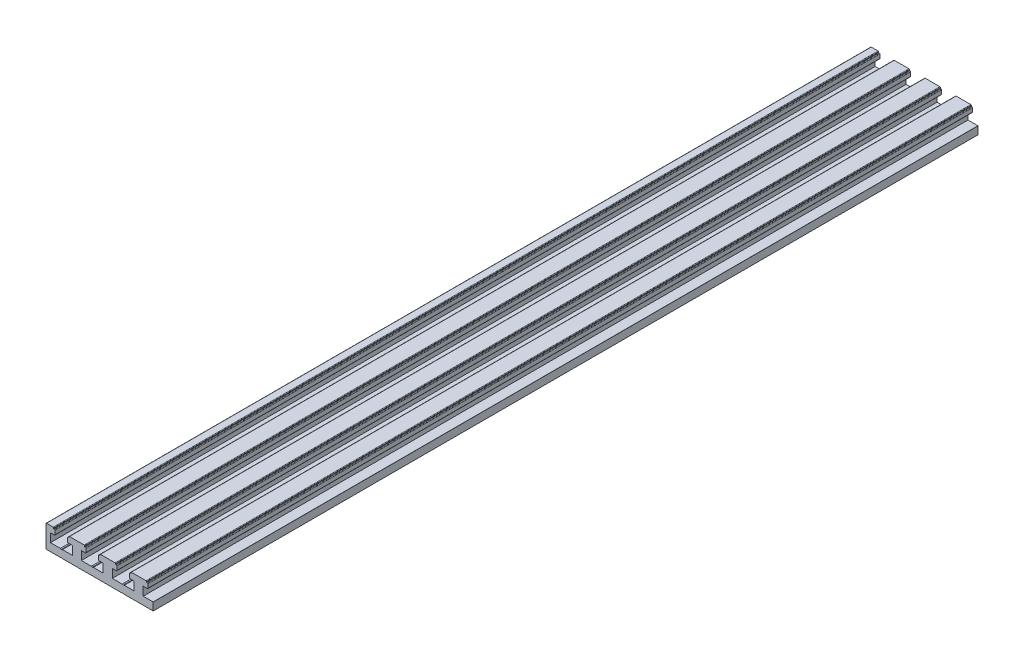
SolidWorks part; units mm, degrees
material "6105 Alloy"
ref_plane "Front Plane" through (0, 0, 0) normal (0, 0, 1) x (1, 0, 0)
ref_plane "Top Plane" through (0, 0, 0) normal (0, 1, 0) x (1, 0, 0)
ref_plane "Right Plane" through (0, 0, 0) normal (1, 0, 0) x (0, 0, -1)
sketch "Sketch1" plane through (0, 0, 0) normal (0, 0, -1) x (-1, 0, 0)
  line L0 (0, 1.72) -> (0, -1.72) construction
  line L1 (-37.45, 8.85) -> (-37.45, -1.65)
  line L2 (-37.2, -1.9) -> (-30.5436, -1.9)
  line L3 (-30.4589, -1.8852) -> (-30, -1.72)
  line L4 (-30, -1.72) -> (-29.5411, -1.8852)
  line L5 (-29.4564, -1.9) -> (-15.5436, -1.9)
  line L6 (-15.4589, -1.8852) -> (-15, -1.72)
  line L7 (-15, -1.72) -> (-14.5411, -1.8852)
  line L8 (-14.4564, -1.9) -> (-0.5436, -1.9)
  line L9 (-0.4589, -1.8852) -> (0, -1.72)
  line L10 (0, -1.72) -> (0.4589, -1.8852)
  line L11 (0.5436, -1.9) -> (14.4564, -1.9)
  line L12 (14.5411, -1.8852) -> (15, -1.72)
  line L13 (15, -1.72) -> (15.4589, -1.8852)
  line L14 (15.5436, -1.9) -> (29.4564, -1.9)
  line L15 (29.5411, -1.8852) -> (30, -1.72)
  line L16 (30, -1.72) -> (30.4589, -1.8852)
  line L17 (30.5436, -1.9) -> (37.2, -1.9)
  line L18 (37.45, -1.65) -> (37.45, 8.85)
  line L19 (37.2, 9.1) -> (33.95, 9.1)
  line L20 (33.7, 8.85) -> (33.7, 8.5)
  line L21 (33.7, 8.5) -> (33.32, 8.5)
  line L22 (33.07, 8.25) -> (33.07, 6.35)
  line L23 (33.32, 6.1) -> (35.3, 6.1)
  line L24 (35.3, 6.1) -> (35.3, 1.9)
  line L25 (35.3, 1.9) -> (30.5436, 1.9)
  line L26 (30.4589, 1.8852) -> (30, 1.72)
  line L27 (30, 1.72) -> (29.5411, 1.8852)
  line L28 (29.4564, 1.9) -> (24.7, 1.9)
  line L29 (24.7, 1.9) -> (24.7, 6.1)
  line L30 (24.7, 6.1) -> (26.68, 6.1)
  line L31 (26.93, 6.35) -> (26.93, 8.25)
  line L32 (26.68, 8.5) -> (26.3, 8.5)
  line L33 (26.3, 8.5) -> (26.3, 8.85)
  line L34 (26.05, 9.1) -> (18.95, 9.1)
  line L35 (18.7, 8.85) -> (18.7, 8.5)
  line L36 (18.7, 8.5) -> (18.32, 8.5)
  line L37 (18.07, 8.25) -> (18.07, 6.35)
  line L38 (18.32, 6.1) -> (20.3, 6.1)
  line L39 (20.3, 6.1) -> (20.3, 1.9)
  line L40 (20.3, 1.9) -> (15.5436, 1.9)
  line L41 (15.4589, 1.8852) -> (15, 1.72)
  line L42 (15, 1.72) -> (14.5411, 1.8852)
  line L43 (14.4564, 1.9) -> (9.7, 1.9)
  line L44 (9.7, 1.9) -> (9.7, 6.1)
  line L45 (9.7, 6.1) -> (11.68, 6.1)
  line L46 (11.93, 6.35) -> (11.93, 8.25)
  line L47 (11.68, 8.5) -> (11.3, 8.5)
  line L48 (11.3, 8.5) -> (11.3, 8.85)
  line L49 (11.05, 9.1) -> (3.95, 9.1)
  line L50 (3.7, 8.85) -> (3.7, 8.5)
  line L51 (3.7, 8.5) -> (3.32, 8.5)
  line L52 (3.07, 8.25) -> (3.07, 6.35)
  line L53 (3.32, 6.1) -> (5.3, 6.1)
  line L54 (5.3, 6.1) -> (5.3, 1.9)
  line L55 (5.3, 1.9) -> (0.5436, 1.9)
  line L56 (0.4589, 1.8852) -> (0, 1.72)
  line L57 (0, 1.72) -> (-0.4589, 1.8852)
  line L58 (-0.5436, 1.9) -> (-5.3, 1.9)
  line L59 (-5.3, 1.9) -> (-5.3, 6.1)
  line L60 (-5.3, 6.1) -> (-3.32, 6.1)
  line L61 (-3.07, 6.35) -> (-3.07, 8.25)
  line L62 (-3.32, 8.5) -> (-3.7, 8.5)
  line L63 (-3.7, 8.5) -> (-3.7, 8.85)
  line L64 (-3.95, 9.1) -> (-11.05, 9.1)
  line L65 (-11.3, 8.85) -> (-11.3, 8.5)
  line L66 (-11.3, 8.5) -> (-11.68, 8.5)
  line L67 (-11.93, 8.25) -> (-11.93, 6.35)
  line L68 (-11.68, 6.1) -> (-9.7, 6.1)
  line L69 (-9.7, 6.1) -> (-9.7, 1.9)
  line L70 (-9.7, 1.9) -> (-14.4564, 1.9)
  line L71 (-14.5411, 1.8852) -> (-15, 1.72)
  line L72 (-15, 1.72) -> (-15.4589, 1.8852)
  line L73 (-15.5436, 1.9) -> (-20.3, 1.9)
  line L74 (-20.3, 1.9) -> (-20.3, 6.1)
  line L75 (-20.3, 6.1) -> (-18.32, 6.1)
  line L76 (-18.07, 6.35) -> (-18.07, 8.25)
  line L77 (-18.32, 8.5) -> (-18.7, 8.5)
  line L78 (-18.7, 8.5) -> (-18.7, 8.85)
  line L79 (-18.95, 9.1) -> (-26.05, 9.1)
  line L80 (-26.3, 8.85) -> (-26.3, 8.5)
  line L81 (-26.3, 8.5) -> (-26.68, 8.5)
  line L82 (-26.93, 8.25) -> (-26.93, 6.35)
  line L83 (-26.68, 6.1) -> (-24.7, 6.1)
  line L84 (-24.7, 6.1) -> (-24.7, 1.9)
  line L85 (-24.7, 1.9) -> (-29.4564, 1.9)
  line L86 (-29.5411, 1.8852) -> (-30, 1.72)
  line L87 (-30, 1.72) -> (-30.4589, 1.8852)
  line L88 (-30.5436, 1.9) -> (-35.3, 1.9)
  line L89 (-35.3, 1.9) -> (-35.3, 6.1)
  line L90 (-35.3, 6.1) -> (-33.32, 6.1)
  line L91 (-33.07, 6.35) -> (-33.07, 8.25)
  line L92 (-33.32, 8.5) -> (-33.7, 8.5)
  line L93 (-33.7, 8.5) -> (-33.7, 8.85)
  line L94 (-33.95, 9.1) -> (-37.2, 9.1)
  arc A0 (-37.45, -1.65) -> (-37.2, -1.9) centre (-37.2, -1.65) ccw
  arc A1 (-30.5436, -1.9) -> (-30.4589, -1.8852) centre (-30.5436, -1.65) ccw
  arc A2 (-29.5411, -1.8852) -> (-29.4564, -1.9) centre (-29.4564, -1.65) ccw
  arc A3 (-15.5436, -1.9) -> (-15.4589, -1.8852) centre (-15.5436, -1.65) ccw
  arc A4 (-14.5411, -1.8852) -> (-14.4564, -1.9) centre (-14.4564, -1.65) ccw
  arc A5 (-0.5436, -1.9) -> (-0.4589, -1.8852) centre (-0.5436, -1.65) ccw
  arc A6 (0.4589, -1.8852) -> (0.5436, -1.9) centre (0.5436, -1.65) ccw
  arc A7 (14.4564, -1.9) -> (14.5411, -1.8852) centre (14.4564, -1.65) ccw
  arc A8 (15.4589, -1.8852) -> (15.5436, -1.9) centre (15.5436, -1.65) ccw
  arc A9 (29.4564, -1.9) -> (29.5411, -1.8852) centre (29.4564, -1.65) ccw
  arc A10 (30.4589, -1.8852) -> (30.5436, -1.9) centre (30.5436, -1.65) ccw
  arc A11 (37.2, -1.9) -> (37.45, -1.65) centre (37.2, -1.65) ccw
  arc A12 (37.45, 8.85) -> (37.2, 9.1) centre (37.2, 8.85) ccw
  arc A13 (33.95, 9.1) -> (33.7, 8.85) centre (33.95, 8.85) ccw
  arc A14 (33.32, 8.5) -> (33.07, 8.25) centre (33.32, 8.25) ccw
  arc A15 (33.07, 6.35) -> (33.32, 6.1) centre (33.32, 6.35) ccw
  arc A16 (30.5436, 1.9) -> (30.4589, 1.8852) centre (30.5436, 1.65) ccw
  arc A17 (29.5411, 1.8852) -> (29.4564, 1.9) centre (29.4564, 1.65) ccw
  arc A18 (26.68, 6.1) -> (26.93, 6.35) centre (26.68, 6.35) ccw
  arc A19 (26.93, 8.25) -> (26.68, 8.5) centre (26.68, 8.25) ccw
  arc A20 (26.3, 8.85) -> (26.05, 9.1) centre (26.05, 8.85) ccw
  arc A21 (18.95, 9.1) -> (18.7, 8.85) centre (18.95, 8.85) ccw
  arc A22 (18.32, 8.5) -> (18.07, 8.25) centre (18.32, 8.25) ccw
  arc A23 (18.07, 6.35) -> (18.32, 6.1) centre (18.32, 6.35) ccw
  arc A24 (15.5436, 1.9) -> (15.4589, 1.8852) centre (15.5436, 1.65) ccw
  arc A25 (14.5411, 1.8852) -> (14.4564, 1.9) centre (14.4564, 1.65) ccw
  arc A26 (11.68, 6.1) -> (11.93, 6.35) centre (11.68, 6.35) ccw
  arc A27 (11.93, 8.25) -> (11.68, 8.5) centre (11.68, 8.25) ccw
  arc A28 (11.3, 8.85) -> (11.05, 9.1) centre (11.05, 8.85) ccw
  arc A29 (3.95, 9.1) -> (3.7, 8.85) centre (3.95, 8.85) ccw
  arc A30 (3.32, 8.5) -> (3.07, 8.25) centre (3.32, 8.25) ccw
  arc A31 (3.07, 6.35) -> (3.32, 6.1) centre (3.32, 6.35) ccw
  arc A32 (0.5436, 1.9) -> (0.4589, 1.8852) centre (0.5436, 1.65) ccw
  arc A33 (-0.4589, 1.8852) -> (-0.5436, 1.9) centre (-0.5436, 1.65) ccw
  arc A34 (-3.32, 6.1) -> (-3.07, 6.35) centre (-3.32, 6.35) ccw
  arc A35 (-3.07, 8.25) -> (-3.32, 8.5) centre (-3.32, 8.25) ccw
  arc A36 (-3.7, 8.85) -> (-3.95, 9.1) centre (-3.95, 8.85) ccw
  arc A37 (-11.05, 9.1) -> (-11.3, 8.85) centre (-11.05, 8.85) ccw
  arc A38 (-11.68, 8.5) -> (-11.93, 8.25) centre (-11.68, 8.25) ccw
  arc A39 (-11.93, 6.35) -> (-11.68, 6.1) centre (-11.68, 6.35) ccw
  arc A40 (-14.4564, 1.9) -> (-14.5411, 1.8852) centre (-14.4564, 1.65) ccw
  arc A41 (-15.4589, 1.8852) -> (-15.5436, 1.9) centre (-15.5436, 1.65) ccw
  arc A42 (-18.32, 6.1) -> (-18.07, 6.35) centre (-18.32, 6.35) ccw
  arc A43 (-18.07, 8.25) -> (-18.32, 8.5) centre (-18.32, 8.25) ccw
  arc A44 (-18.7, 8.85) -> (-18.95, 9.1) centre (-18.95, 8.85) ccw
  arc A45 (-26.05, 9.1) -> (-26.3, 8.85) centre (-26.05, 8.85) ccw
  arc A46 (-26.68, 8.5) -> (-26.93, 8.25) centre (-26.68, 8.25) ccw
  arc A47 (-26.93, 6.35) -> (-26.68, 6.1) centre (-26.68, 6.35) ccw
  arc A48 (-29.4564, 1.9) -> (-29.5411, 1.8852) centre (-29.4564, 1.65) ccw
  arc A49 (-30.4589, 1.8852) -> (-30.5436, 1.9) centre (-30.5436, 1.65) ccw
  arc A50 (-33.32, 6.1) -> (-33.07, 6.35) centre (-33.32, 6.35) ccw
  arc A51 (-33.07, 8.25) -> (-33.32, 8.5) centre (-33.32, 8.25) ccw
  arc A52 (-33.7, 8.85) -> (-33.95, 9.1) centre (-33.95, 8.85) ccw
  arc A53 (-37.2, 9.1) -> (-37.45, 8.85) centre (-37.2, 8.85) ccw
  point P2 (0, 0)
  dimension "D1" = 11
  dimension "D2" = 74.9
extrude "RawPart" add sketch "Sketch1" against normal blind 400
hole_wizard "CSK for M3 Flat Head Machine Screw1" positions "3DSketch1" profile "Sketch2" countersink size "M3" standard "ANSI Metric" end condition through all
sketch3d "3DSketch1"
  point P0 (-30, 1.9, 65)
  point P2 (0, 1.9, 65)
  point P35 (0, 1.9, 330)
  point P37 (-30, 1.9, 330)
  dimension "D4" = 330
  dimension "D1" = 65
  dimension "D2" = 7.45
  dimension "D3" = 30
sketch "Sketch2" plane through (-30, 1.9, 65) normal (1, 0, 0) x (0, 0, 1)
  line L0 (0, 0) -> (0, 3.8)
  line L1 (0, 3.8) -> (1.6, 3.8)
  line L2 (1.6, 3.8) -> (1.6, 1.9)
  line L3 (1.6, 1.9) -> (3, 0.5)
  line L4 (3, 0.5) -> (3, 0)
  line L6 (3, 0) -> (0, 0)
  line L7 (-1.6, 1.9) -> (-3, 0.5) construction
  line L11 (0, -6.35) -> (0, 107.95) construction
  dimension "Thru Hole Dia." = 3.2
  dimension "Thru Hole Depth" = 3.8
  dimension "C'Sink Dia." = 6
  dimension "C'Sink Angle" = 90
  dimension "Head Clearance" = 0.5
hole_wizard "M4x0.7 Tapped Hole1" [suppressed] positions "Sketch4" profile "Sketch5" tap size "M4x0.7" standard "ANSI Metric"
sketch "Sketch4" plane through (0, 1.9, 0) normal (0, 1, 0) x (1, 0, 0)
  line L1 (-0.5436, 0) -> (-14.4564, 0) construction
  line L2 (-37.45, -400) -> (-37.45, 0) construction
  line L3 (15, -400) -> (15, 0) construction
  line L5 (-26.05, 0) -> (-18.95, 0) construction
  point P0 (15, -30)
  point P15 (15, -372)
  dimension "D1" = 30
  dimension "D2" = 52.45
  dimension "D3" = 372
sketch "Sketch5" plane through (15, 1.9, 30) normal (1, 0, 0) x (0, 0, 1)
  line L0 (0, 0) -> (0, 3.8)
  line L1 (0, 3.8) -> (1.65, 3.8)
  line L2 (1.65, 3.8) -> (1.65, 0)
  line L5 (1.65, 0) -> (0, 0)
  line L11 (0, -6.35) -> (0, 107.95) construction
  dimension "Thru Tap Drill Dia." = 3.3
  dimension "Thru Tap Drill Depth" = 3.8
cosmetic thread "Hole Thread4" [suppressed] parameters "D2"=4
cosmetic thread "Hole Thread10" [suppressed] parameters "D2"=4
sketch "Sketch6" plane through (0, 0, 0) normal (0, 0, -1) x (-1, 0, 0)
  line L0 (37.45, -1.65) -> (37.45, 8.85) construction
  line L1 (-14.55, -9.9057) -> (-41.3993, -9.9057)
  line L2 (-14.55, -9.9057) -> (-14.55, 14.5956)
  line L3 (-14.55, 14.5956) -> (-41.3993, 14.5956)
  line L4 (-41.3993, -9.9057) -> (-41.3993, 14.5956)
  dimension "D1" = 52
extrude "CutUnnecessaryHalf" cut sketch "Sketch6" against normal through all
equation "\"D4@3DSketch1\" = \"D1@RawPart\" - \"D1@3DSketch1\" - 5"
